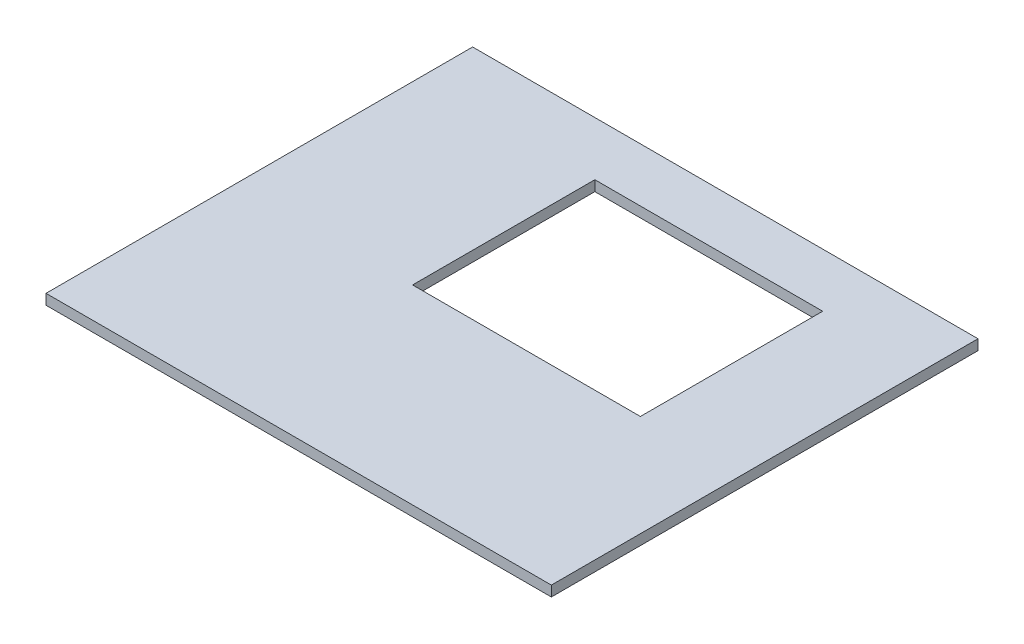
SolidWorks part; units mm, degrees
material "Custom Plastic"
ref_plane "Front Plane" through (0, 0, 0) normal (0, 0, 1) x (1, 0, 0)
ref_plane "Top Plane" through (0, 0, 0) normal (0, 1, 0) x (1, 0, 0)
ref_plane "Right Plane" through (0, 0, 0) normal (1, 0, 0) x (0, 0, -1)
sketch "Sketch1" plane through (0, 0, 0) normal (0, 1, 0) x (1, 0, 0)
  line L1 (-59.5, -51.5) -> (59.5, -51.5)
  line L2 (-59.5, -51.5) -> (-59.5, 51.5)
  line L3 (-59.5, 51.5) -> (59.5, 51.5)
  line L4 (59.5, -51.5) -> (59.5, 51.5)
  line L5 (-59.5, -51.5) -> (59.5, 51.5) construction
  line L6 (-59.5, 51.5) -> (59.5, -51.5) construction
  point P0 (0, 0)
  dimension "D1" = 119
  dimension "D2" = 103
extrude "Boss-Extrude1" add sketch "Sketch1" along normal blind 2.5
sketch "Sketch3" plane through (0, 2.5, 0) normal (0, 1, 0) x (1, 0, 0)
  line L0 (-59.5, -51.5) -> (59.5, -51.5) construction
  line L1 (-18.5, -5.5) -> (36.5, -5.5)
  line L2 (-18.5, -5.5) -> (-18.5, 38.5)
  line L3 (-18.5, 38.5) -> (36.5, 38.5)
  line L4 (36.5, -5.5) -> (36.5, 38.5)
  line L5 (-18.5, -5.5) -> (36.5, 38.5) construction
  line L6 (-18.5, 38.5) -> (36.5, -5.5) construction
  line L7 (-59.5, 51.5) -> (-59.5, -51.5) construction
  point P0 (9, 16.5)
  dimension "D1" = 46
  dimension "D2" = 41
  dimension "D3" = 44
  dimension "D4" = 55
extrude "Cut-Extrude2" cut sketch "Sketch3" against normal blind 10
sketch "Sketch4" plane through (-59.5, 0, 0) normal (-1, 0, 0) x (0, 0, 1)
  line L4 (-51.5, 0) -> (51.5, 0)
  line L5 (51.5, 0) -> (51.5, 2.5)
  line L6 (51.5, 2.5) -> (-51.5, 2.5)
  line L7 (-51.5, 2.5) -> (-51.5, 0)
  line L8 (-51.5, 0) -> (51.5, 0)
  line L9 (51.5, 0) -> (51.5, 2.5)
  line L10 (51.5, 2.5) -> (-51.5, 2.5)
  line L11 (-51.5, 2.5) -> (-51.5, 0)
  dimension "D1" = 0
extrude "Boss-Extrude2" add sketch "Sketch4" along normal blind 1.5
sketch "Sketch5" plane through (59.5, 0, 0) normal (1, 0, 0) x (0, 0, -1)
  line L4 (-51.5, 0) -> (51.5, 0)
  line L5 (51.5, 0) -> (51.5, 2.5)
  line L6 (51.5, 2.5) -> (-51.5, 2.5)
  line L7 (-51.5, 2.5) -> (-51.5, 0)
  line L8 (-51.5, 0) -> (51.5, 0)
  line L9 (51.5, 0) -> (51.5, 2.5)
  line L10 (51.5, 2.5) -> (-51.5, 2.5)
  line L11 (-51.5, 2.5) -> (-51.5, 0)
  dimension "D1" = 0
extrude "Boss-Extrude3" add sketch "Sketch5" along normal blind 1.5
